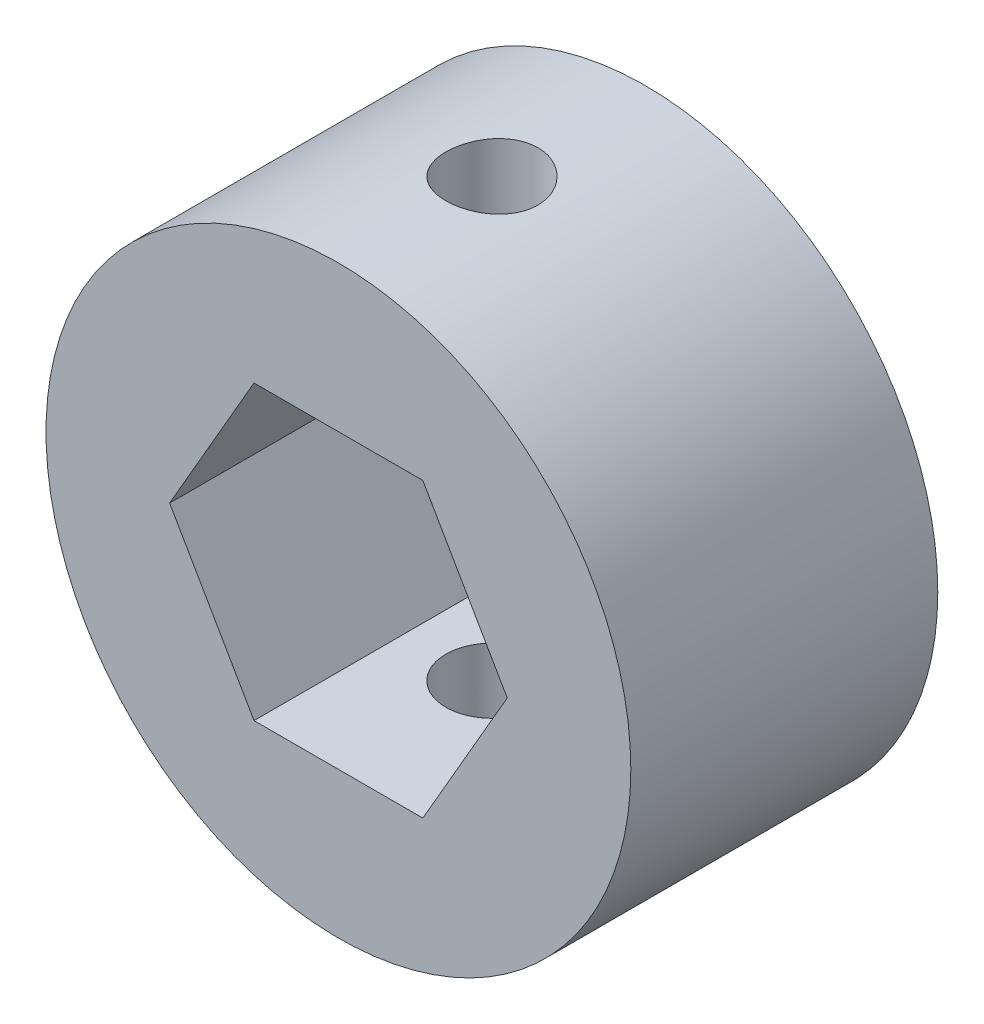
SolidWorks part; units mm, degrees
ref_plane "Front Plane" through (0, 0, 0) normal (0, 0, 1) x (1, 0, 0)
ref_plane "Top Plane" through (0, 0, 0) normal (0, 1, 0) x (1, 0, 0)
ref_plane "Right Plane" through (0, 0, 0) normal (1, 0, 0) x (0, 0, -1)
sketch "Sketch2" plane through (0, 0, 0) normal (0, 0, 1) x (1, 0, 0)
  line L1 (5.4993, 0) -> (2.7496, 4.7625)
  line L2 (2.7496, 4.7625) -> (-2.7496, 4.7625)
  line L3 (-2.7496, 4.7625) -> (-5.4993, 0)
  line L4 (-5.4993, 0) -> (-2.7496, -4.7625)
  line L5 (-2.7496, -4.7625) -> (2.7496, -4.7625)
  line L6 (2.7496, -4.7625) -> (5.4993, 0)
  circle A0 centre (0, 0) radius 4.7625 construction
  circle A1 centre (0, 0) radius 9.525
  dimension "D1" = 19.05
extrude "Boss-Extrude1" add sketch "Sketch2" along normal blind 10
sketch "Sketch3" plane through (0, -4.7625, 0) normal (0, 1, 0) x (1, 0, 0)
  line L1 (2.7496, -10) -> (2.7496, 0) construction
  circle A0 centre (0, -5) radius 1.5
  point P2 (0, -5)
  point P6 (2.7496, -5)
  dimension "D1" = 3
extrude "Cut-Extrude1" cut sketch "Sketch3" against normal through all and the other way through all contours A0
